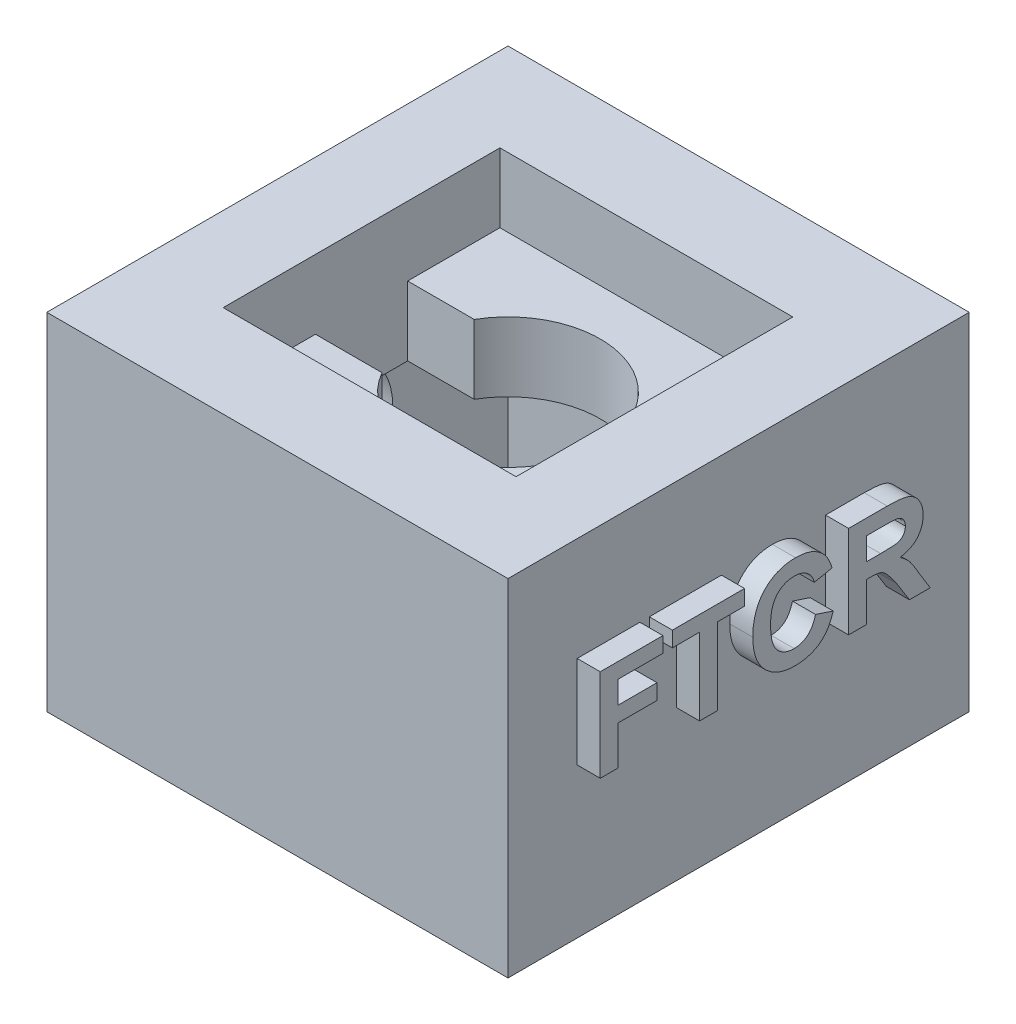
SolidWorks part; units mm, degrees
ref_plane "Спереди" through (0, 0, 0) normal (0, 0, 1) x (1, 0, 0)
ref_plane "Сверху" through (0, 0, 0) normal (0, 1, 0) x (1, 0, 0)
ref_plane "Справа" through (0, 0, 0) normal (1, 0, 0) x (0, 0, -1)
sketch "Sketch6" plane through (0, 0, 0) normal (0, 1, 0) x (1, 0, 0)
  line L1 (10, -10) -> (-10, -10)
  line L2 (10, -10) -> (10, 10)
  line L3 (10, 10) -> (-10, 10)
  line L4 (-10, -10) -> (-10, 10)
  line L5 (10, -10) -> (-10, 10) construction
  line L6 (10, 10) -> (-10, -10) construction
  point P0 (0, 0)
  dimension "D1" = 20
extrude "Boss-Extrude3" add sketch "Sketch6" along normal blind 15
sketch "Sketch7" plane through (0, 15, 0) normal (0, 1, 0) x (1, 0, 0)
  line L4 (6.35, -6) -> (-6.35, -6)
  line L5 (6.35, -6) -> (6.35, 6)
  line L6 (6.35, 6) -> (-6.35, 6)
  line L7 (-6.35, -6) -> (-6.35, 6)
  line L8 (6.35, -6) -> (-6.35, 6) construction
  line L9 (6.35, 6) -> (-6.35, -6) construction
  point P6 (0, 0)
  dimension "D1" = 12
  dimension "D2" = 12.7
extrude "Cut-Extrude2" cut sketch "Sketch7" against normal blind 3
sketch "Sketch8" plane through (0, 0, 0) normal (0, -1, 0) x (1, 0, 0)
  line L1 (8, -8) -> (-8, -8)
  line L2 (8, -8) -> (8, 8)
  line L3 (8, 8) -> (-8, 8)
  line L4 (-8, -8) -> (-8, 8)
  line L5 (8, -8) -> (-8, 8) construction
  line L6 (8, 8) -> (-8, -8) construction
  point P0 (0, 0)
  dimension "D1" = 16
extrude "Cut-Extrude3" cut sketch "Sketch8" against normal offset from surface (9 mm away) 3 up to face at (0, 12, 0)
sketch "Sketch9" plane through (0, 12, 0) normal (0, 1, 0) x (1, 0, 0)
  circle A0 centre (0, 0) radius 4
  dimension "D1" = 8
extrude "Cut-Extrude4" cut sketch "Sketch9" against normal through all
sketch "Sketch10" plane through (0, 12, 0) normal (0, 1, 0) x (1, 0, 0)
  line L0 (-6.35, 6) -> (-6.35, -6) construction
  line L1 (6.35, -2) -> (-6.35, -2)
  line L2 (6.35, -2) -> (6.35, 2)
  line L3 (6.35, 2) -> (-6.35, 2)
  line L4 (-6.35, -2) -> (-6.35, 2)
  line L5 (6.35, -2) -> (-6.35, 2) construction
  line L6 (6.35, 2) -> (-6.35, -2) construction
  point P0 (0, 0)
  dimension "D1" = 4
extrude "Cut-Extrude5" cut sketch "Sketch10" against normal through all
sketch "Sketch11" plane through (-8, 0, 0) normal (1, 0, 0) x (0, 0, -1)
  line L0 (0, 9) -> (0, 0) construction
  line L1 (-8, 9) -> (8, 9) construction
  line L2 (-8, 0) -> (8, 0) construction
  circle A0 centre (0, 6) radius 3
  dimension "D1" = 6
extrude "Cut-Extrude6" cut sketch "Sketch11" against normal through all
sketch "Sketch12" plane through (10, 0, 0) normal (1, 0, 0) x (0, 0, -1)
  line L0 (-10, 6.5) -> (10, 6.5) construction
  line L1 (-10, 15) -> (-10, 0) construction
  line L2 (10, 15) -> (10, 0) construction
  line L3 (-10, 15) -> (10, 15) construction
  text T0 "<b>FTCR</b>"
  dimension "D1" = 8.5
extrude "Boss-Extrude4" add sketch "Sketch12" along normal blind 1
